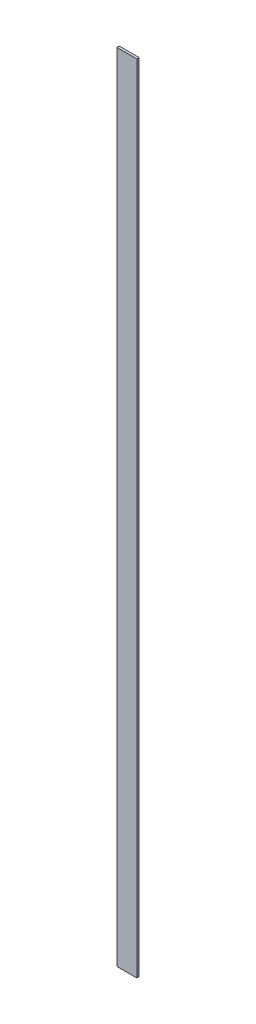
SolidWorks part; units mm, degrees
ref_plane "Front Plane" through (0, 0, 0) normal (0, 0, 1) x (1, 0, 0)
ref_plane "Top Plane" through (0, 0, 0) normal (0, 1, 0) x (1, 0, 0)
ref_plane "Right Plane" through (0, 0, 0) normal (1, 0, 0) x (0, 0, -1)
sketch "Sketch1" plane through (0, 0, 0) normal (0, 0, 1) x (1, 0, 0)
  line L1 (-2.5, -100) -> (2.5, -100)
  line L2 (-2.5, -100) -> (-2.5, 100)
  line L3 (-2.5, 100) -> (2.5, 100)
  line L4 (2.5, -100) -> (2.5, 100)
  line L5 (-2.5, -100) -> (2.5, 100) construction
  line L6 (-2.5, 100) -> (2.5, -100) construction
  point P0 (0, 0)
  dimension "D1" = 200
  dimension "D2" = 5
extrude "Boss-Extrude1" add sketch "Sketch1" along normal blind 0.6
